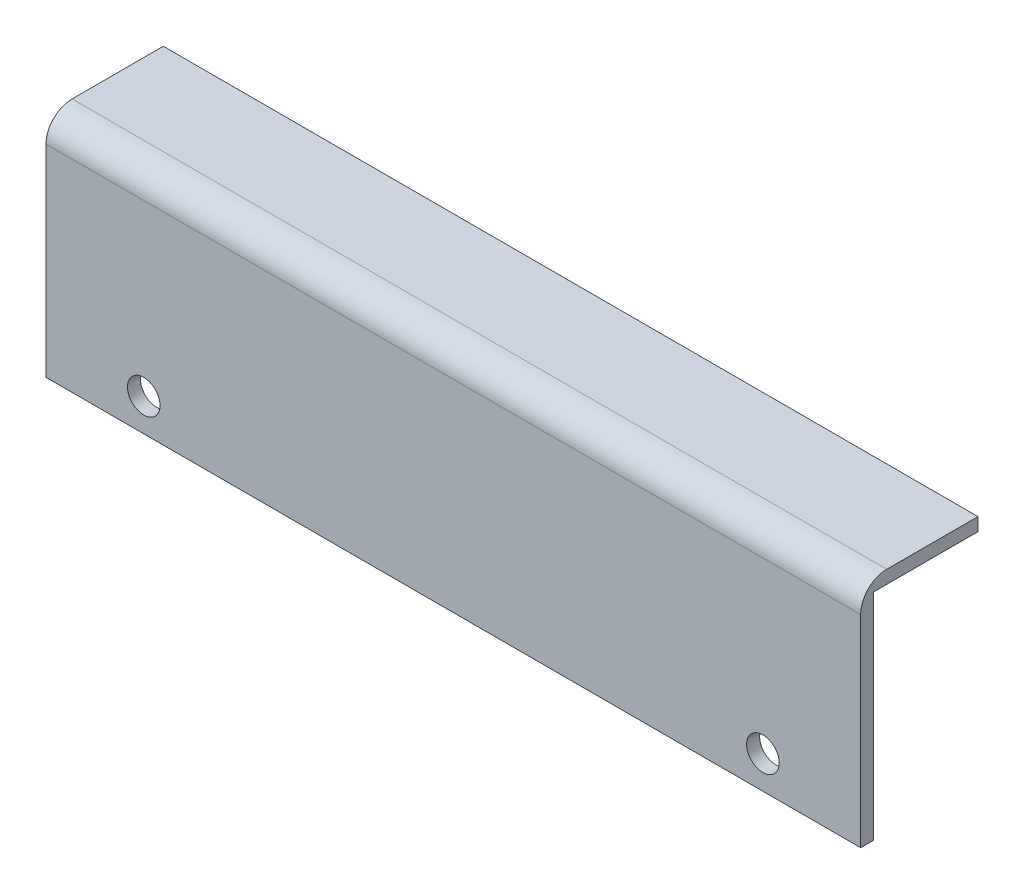
SolidWorks part; units mm, degrees
ref_plane "Front Plane" through (0, 0, 0) normal (0, 0, 1) x (1, 0, 0)
ref_plane "Top Plane" through (0, 0, 0) normal (0, 1, 0) x (1, 0, 0)
ref_plane "Right Plane" through (0, 0, 0) normal (1, 0, 0) x (0, 0, -1)
sketch "Sketch1" plane through (0, 0, 0) normal (1, 0, 0) x (0, 0, -1)
  line L0 (1.1416, 16.7868) -> (17.1416, 16.7868)
  line L3 (-0.8584, -16.2132) -> (1.1416, -16.2132)
  line L4 (1.1416, 16.7868) -> (1.1416, -16.2132)
  line L5 (-0.8584, 18.7868) -> (-0.8584, -16.2132)
  line L7 (-0.8584, 18.7868) -> (17.1416, 18.7868)
  line L10 (17.1416, 18.7868) -> (17.1416, 16.7868)
  point P0 (0, 0)
  dimension "D1" = 35
  dimension "D2" = 18
  dimension "D3" = 2
  dimension "D4" = 2
extrude "Boss-Extrude1" add sketch "Sketch1" along normal blind 125
fillet "Fillet1" radius 4 1 edges at (62.5, 18.7868, 0.8584)
sketch "Sketch2" plane through (0, 0, -1.1416) normal (0, 0, -1) x (-1, 0, 0)
  line L0 (-125, -16.2132) -> (0, -16.2132) construction
  line L2 (0, -16.2132) -> (0, 16.7868) construction
  line L3 (-125, -16.2132) -> (-125, 16.7868) construction
  circle A0 centre (-110, -11.2132) radius 2.5
  circle A1 centre (-15, -11.2132) radius 2.5
  point P8 (0, -8.5385)
  dimension "D1" = 5
  dimension "D2" = 5
  dimension "D3" = 15
  dimension "D4" = 15
extrude "Cut-Extrude1" cut sketch "Sketch2" against normal blind 125
